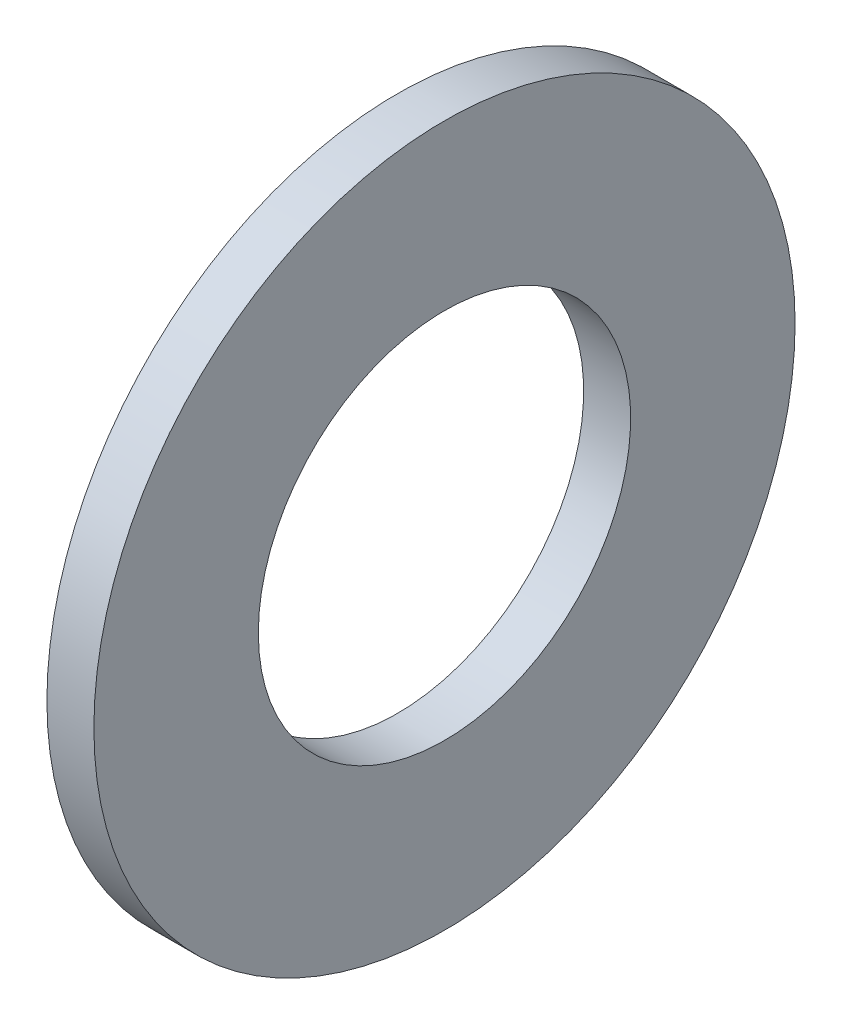
SolidWorks part; units mm, degrees
ref_plane "Plane1" through (0, 0, 0) normal (0, 0, 1) x (1, 0, 0)
ref_plane "Plane2" through (0, 0, 0) normal (0, 1, 0) x (1, 0, 0)
ref_plane "Plane3" through (0, 0, 0) normal (1, 0, 0) x (0, 0, -1)
sketch "Sketch1" plane through (0, 0, 0) normal (0, 0, 1) x (1, 0, 0)
  line L0 (-34.925, 0) -> (9.525, 0) construction
  line L1 (0, 13.4874) -> (0, 25.4)
  line L2 (0, 25.4) -> (-3.4036, 25.4)
  line L3 (-3.4036, 25.4) -> (-3.4036, 13.4874)
  line L4 (-3.4036, 13.4874) -> (0, 13.4874)
  dimension "Thickness" = 3.4036
  dimension "Inside_dia" = 26.9748
  dimension "Outside_dia" = 50.8
revolve "Base-Revolve" add sketch "Sketch1" angle 360 about L0
